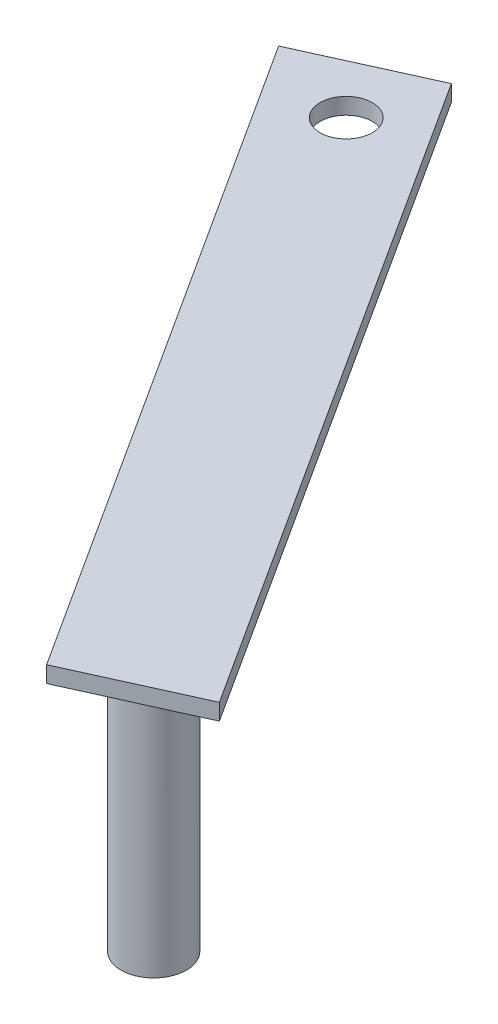
SolidWorks part; units mm, degrees
ref_plane "Front" through (0, 0, 0) normal (0, 0, 1) x (1, 0, 0)
ref_plane "Top" through (0, 0, 0) normal (0, 1, 0) x (1, 0, 0)
ref_plane "Right" through (0, 0, 0) normal (1, 0, 0) x (0, 0, -1)
sketch "Sketch1" plane through (0, 0, 0) normal (0, 1, 0) x (1, 0, 0)
  line L0 (-46.7772, -53.7198) -> (-128.4608, 73.101)
  line L1 (-128.4608, 73.101) -> (-105.3198, 83.5727)
  line L2 (-105.3198, 83.5727) -> (-23.6363, -43.2481)
  line L3 (-23.6363, -43.2481) -> (-46.7772, -53.7198)
  circle A0 centre (-109.8116, 67.6003) radius 5.0783
  dimension "D1" = 25.4
  dimension "D2" = 25.4
  dimension "D3" = 150.85
  dimension "D4" = 12.7
  dimension "D5" = 12.7
extrude "Boss-Extrude1" add sketch "Sketch1" along normal blind 3.175
sketch "Sketch2" plane through (0, 3.175, 0) normal (0, 1, 0) x (1, 0, 0)
  line L0 (-46.7772, -53.7198) -> (-23.6363, -43.2481) construction
  line L2 (-128.4608, 73.101) -> (-46.7772, -53.7198) construction
  circle A0 centre (-42.0323, -37.6329) radius 6.35
  dimension "D1" = 12.7
  dimension "D2" = 12.7
  dimension "D3" = 12.7
extrude "Boss-Extrude2" add sketch "Sketch2" against normal blind 53.975
